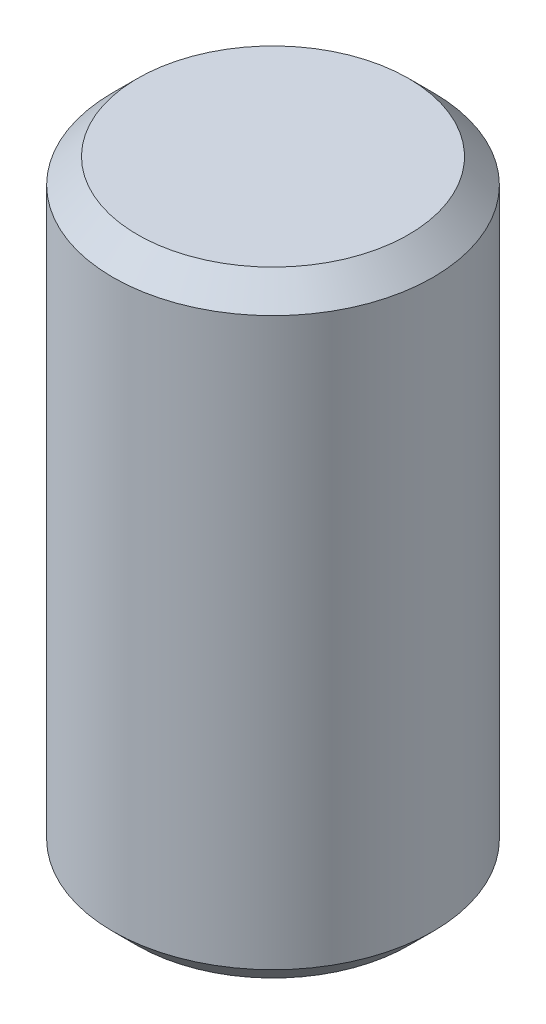
SolidWorks part; units mm, degrees
ref_plane "Front" through (0, 0, 0) normal (0, 0, 1) x (1, 0, 0)
ref_plane "Top" through (0, 0, 0) normal (0, 1, 0) x (1, 0, 0)
ref_plane "Right" through (0, 0, 0) normal (1, 0, 0) x (0, 0, -1)
sketch "Sketch1" plane through (0, 0, 0) normal (0, 0, 1) x (1, 0, 0)
  line L0 (0, 6.0802) -> (0, -6.0802) construction
  line L1 (0, -6.35) -> (3.302, -6.35)
  line L2 (3.302, -6.35) -> (3.302, 6.35)
  line L3 (3.302, 6.35) -> (0, 6.35)
  line L4 (0, 6.35) -> (0, -6.35)
  point P6 (0, 0)
  dimension "D1" = 6.604
  dimension "D2" = 12.7
revolve "Revolve1" add sketch "Sketch1" angle 360 about L0
chamfer "Chamfer1" distance 0.508 angle 45 2 edges at (0, -6.35, 3.302) (0, 6.35, 3.302)
